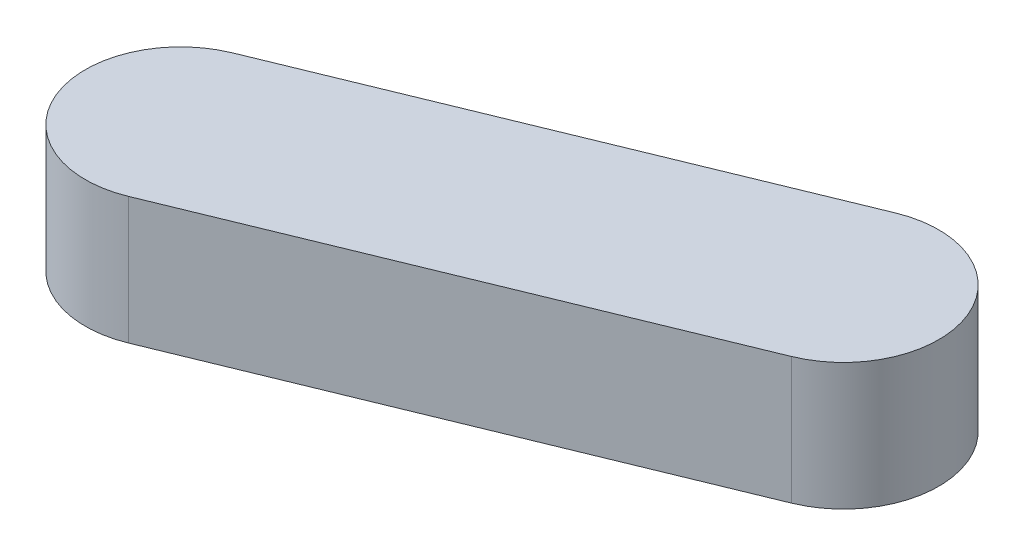
SolidWorks part; units mm, degrees
ref_plane "Front Plane" through (0, 0, 0) normal (0, 0, 1) x (1, 0, 0)
ref_plane "Top Plane" through (0, 0, 0) normal (0, 1, 0) x (1, 0, 0)
ref_plane "Right Plane" through (0, 0, 0) normal (1, 0, 0) x (0, 0, -1)
sketch "Sketch1" plane through (0, 0, 0) normal (0, 1, 0) x (1, 0, 0)
  line L0 (-64.8839, -24.7132) -> (29.1151, 13.8453) construction
  line L1 (-72.1136, -7.0884) -> (21.8854, 31.4701)
  line L2 (-57.6541, -42.338) -> (36.3448, -3.7795)
  arc A0 (-72.1136, -7.0884) -> (-57.6541, -42.338) centre (-64.8839, -24.7132) ccw
  arc A1 (36.3448, -3.7795) -> (21.8854, 31.4701) centre (29.1151, 13.8453) ccw
  point P2 (-17.8844, -5.4339)
  dimension "D1" = 101.6
  dimension "D2" = 38.1
extrude "Boss-Extrude1" add sketch "Sketch1" along normal blind 25.4
